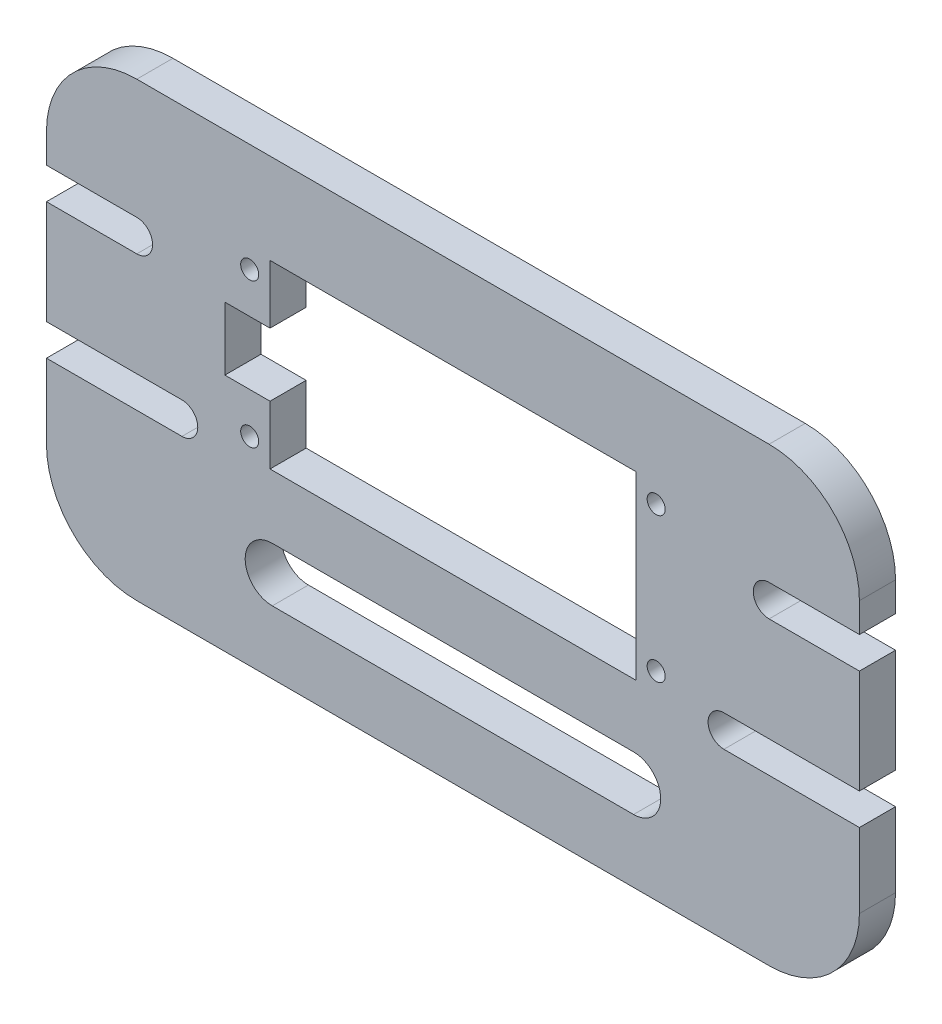
SolidWorks part; units mm, degrees
ref_plane "前视基准面" through (0, 0, 0) normal (0, 0, 1) x (1, 0, 0)
ref_plane "上视基准面" through (0, 0, 0) normal (0, 1, 0) x (1, 0, 0)
ref_plane "右视基准面" through (0, 0, 0) normal (1, 0, 0) x (0, 0, -1)
sketch "草图1" plane through (0, 0, 0) normal (0, 0, 1) x (1, 0, 0)
  line L0 (0, -55) -> (0, 55) construction
  line L1 (-35, -25) -> (35, -25)
  line L2 (-45, -15) -> (-45, 15)
  line L3 (-35, 25) -> (35, 25)
  line L4 (45, -15) -> (45, 15)
  line L5 (-45, -25) -> (45, 25) construction
  line L6 (-45, 25) -> (45, -25) construction
  line L7 (-20, 15) -> (20, 15)
  line L8 (-20, 15) -> (-20, -5)
  line L9 (-20, -5) -> (20, -5)
  line L10 (20, 15) -> (20, -5)
  line L11 (-20, -15) -> (20, -15) construction
  line L12 (-20, -12) -> (20, -12)
  line L13 (-20, -18) -> (20, -18)
  line L14 (-45, -5) -> (-30, -5) construction
  line L15 (-45, -3.25) -> (-30, -3.25)
  line L16 (-45, -6.75) -> (-30, -6.75)
  line L17 (-45, 10) -> (-35, 10) construction
  line L18 (-45, 11.75) -> (-35, 11.75)
  line L19 (-45, 8.25) -> (-35, 8.25)
  line L20 (45, 10) -> (35, 10) construction
  line L21 (45, 8.25) -> (35, 8.25)
  line L22 (45, 11.75) -> (35, 11.75)
  line L23 (45, -5) -> (30, -5) construction
  line L24 (45, -6.75) -> (30, -6.75)
  line L25 (45, -3.25) -> (30, -3.25)
  circle A0 centre (-24, 10) radius 3
  circle A1 centre (-24, 0) radius 3
  circle A2 centre (24, 10) radius 3
  circle A3 centre (24, 0) radius 3
  arc A4 (-20, -12) -> (-20, -18) centre (-20, -15) ccw
  arc A5 (20, -18) -> (20, -12) centre (20, -15) ccw
  arc A6 (35, -25) -> (45, -15) centre (35, -15) ccw
  arc A7 (35, 25) -> (45, 15) centre (35, 15) cw
  arc A8 (-35, -25) -> (-45, -15) centre (-35, -15) cw
  arc A9 (-45, 15) -> (-35, 25) centre (-35, 15) cw
  arc A10 (-45, -3.25) -> (-45, -6.75) centre (-45, -5) ccw
  arc A11 (-30, -6.75) -> (-30, -3.25) centre (-30, -5) ccw
  arc A12 (-45, 11.75) -> (-45, 8.25) centre (-45, 10) ccw
  arc A13 (-35, 8.25) -> (-35, 11.75) centre (-35, 10) ccw
  arc A14 (45, 8.25) -> (45, 11.75) centre (45, 10) ccw
  arc A15 (35, 11.75) -> (35, 8.25) centre (35, 10) ccw
  arc A16 (45, -6.75) -> (45, -3.25) centre (45, -5) ccw
  arc A17 (30, -3.25) -> (30, -6.75) centre (30, -5) ccw
  point P0 (0, 0)
  point P20 (0, -15)
  point P41 (-37.5, -5)
  point P46 (-40, 10)
  point P55 (40, 10)
  point P60 (37.5, -5)
  dimension "D9" = 6
  dimension "D12" = 6
  dimension "D14" = 6
  dimension "D15" = 6
  dimension "D16" = 3
  dimension "D20" = 10
  dimension "D21" = 1.75
  dimension "D22" = 1.75
  dimension "D27" = 1.75
  dimension "D28" = 1.75
  dimension "D1" = 90
  dimension "D2" = 50
  dimension "D3" = 20
  dimension "D4" = 20
  dimension "D5" = 40
  dimension "D6" = 20
  dimension "D7" = 25
  dimension "D8" = 10
  dimension "D10" = 48
  dimension "D11" = 24
  dimension "D13" = 10
  dimension "D17" = 20
  dimension "D18" = 40
  dimension "D19" = 10
  dimension "D23" = 15
  dimension "D24" = 20
  dimension "D25" = 15
  dimension "D26" = 10
  dimension "D29" = 15
  dimension "D30" = 10
  dimension "D31" = 20
extrude "凸台-拉伸1" add sketch "草图1" along normal blind 4 contours A17 L25 L4 L21 A15 L22 A7 L3 A9 L2 L18 A13 L19 L15 A11 L16 A8 L1 A6 L24 A5 L13 A4 L12 A3 A2 A1 A0 L7 L10 L9 L8
sketch "草图2" plane through (0, 0, 4) normal (0, 0, 1) x (1, 0, 0)
  line L0 (20, 5) -> (-20, 5)
  line L1 (-20, 15) -> (20, 15)
  line L2 (-20, 15) -> (-20, -5)
  line L3 (-20, -5) -> (20, -5)
  line L4 (20, 15) -> (20, -5)
  line L6 (-11, 11) -> (11, 11)
  line L7 (-11, 11) -> (-11, -1)
  line L8 (-11, -1) -> (11, -1)
  line L9 (11, 11) -> (11, -1)
  line L10 (-11, 11) -> (11, -1) construction
  line L11 (-11, -1) -> (11, 11) construction
  point P8 (0, 5)
  line M37 (-20, 15) -> (20, 15)
  line M38 (20, 15) -> (20, -5)
  line M39 (20, -5) -> (-20, -5)
  line M40 (-20, -5) -> (-20, 15)
  dimension "D1" = 22
  dimension "D2" = 12
extrude "凸台-拉伸3" add sketch "草图2" against normal blind 4 contours L0 L9 L8 L7 M40 M39 M38 | L6 L9 L0 L7 M38 M37 M40
sketch "草图3" plane through (0, 0, 4) normal (0, 0, 1) x (1, 0, 0)
  circle A0 centre (-24, 10) radius 3
  circle A1 centre (-24, 0) radius 3
  circle A2 centre (24, 10) radius 3
  circle A3 centre (24, 0) radius 3
extrude "凸台-拉伸4" add sketch "草图3" against normal blind 4
sketch "草图4" plane through (0, 0, 4) normal (0, 0, 1) x (1, 0, 0)
  line L0 (-11, 5) -> (-14, 5)
  line L1 (-11, 11) -> (-11, -1) construction
  line L2 (11, 5) -> (14, 5)
  line L3 (11, 11) -> (11, -1) construction
  circle A0 centre (-14, 5) radius 1
  circle A1 centre (14, 5) radius 1
  dimension "D1" = 3
  dimension "D2" = 3
extrude "切除-拉伸1" cut sketch "草图4" against normal blind 4
sketch "草图5" plane through (0, 0, 4) normal (0, 0, 1) x (1, 0, 0)
  line L0 (-30, -5) -> (-22.5, -5)
  line L1 (-22.5, -5) -> (-22.5, -3)
  line L2 (-22.5, -3) -> (-22.5, 13)
  circle A0 centre (-22.5, -3) radius 1
  circle A1 centre (-22.5, 13) radius 1
  dimension "D3" = 16
  dimension "D1" = 7.5
  dimension "D2" = 2
extrude "切除-拉伸2" cut sketch "草图5" against normal through all
mirror "镜向1" about plane through (0, 0, 0) normal (1, 0, 0) of "切除-拉伸2"
sketch "草图6" plane through (0, 0, 4) normal (0, 0, 1) x (1, 0, 0)
  line L1 (-20.25, 15) -> (20.25, 15)
  line L2 (-20.25, 15) -> (-20.25, -5)
  line L3 (-20.25, -5) -> (20.25, -5)
  line L4 (20.25, 15) -> (20.25, -5)
  line L6 (-11, 11) -> (11, 11) construction
  line L8 (-11, 11) -> (-11, -1) construction
  line L10 (-25.25, 8.5) -> (-20.25, 8.5)
  line L11 (-25.25, 8.5) -> (-25.25, 1.5)
  line L12 (-25.25, 1.5) -> (-20.25, 1.5)
  line L13 (-20.25, 8.5) -> (-20.25, 1.5)
  circle M10 centre (-14, 5) radius 1
  circle M11 centre (14, 5) radius 1
  line M40 (-11, 11) -> (11, 11)
  line M41 (11, 11) -> (11, -1)
  line M42 (11, -1) -> (-11, -1)
  line M43 (-11, -1) -> (-11, 11)
  dimension "D1" = 40.5
  dimension "D2" = 20
  dimension "D3" = 4
  dimension "D4" = 9.25
  dimension "D5" = 7
  dimension "D6" = 6.5
  dimension "D7" = 5
extrude "切除-拉伸3" cut sketch "草图6" against normal blind 10 contours L11 L12 L2 L10 | L4 L1 L2 L3 M11 M43 M40 M41 M42 M10
